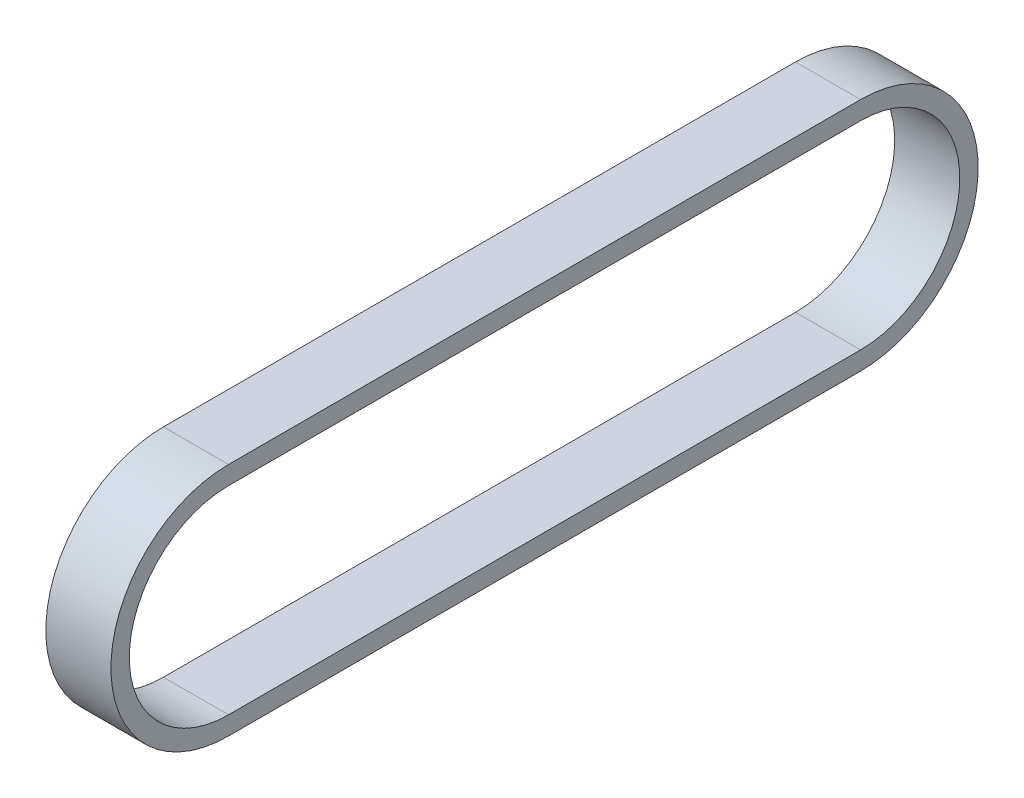
SolidWorks part; units mm, degrees
ref_plane "Front Plane" through (0, 0, 0) normal (0, 0, 1) x (1, 0, 0)
ref_plane "Top Plane" through (0, 0, 0) normal (0, 1, 0) x (1, 0, 0)
ref_plane "Right Plane" through (0, 0, 0) normal (1, 0, 0) x (0, 0, -1)
sketch "Sketch1" plane through (0, 0, 0) normal (1, 0, 0) x (0, 0, -1)
  line L0 (0, 0) -> (87.376, 0) construction
  line L1 (0, -13.716) -> (87.376, -13.716)
  line L2 (0, 13.716) -> (87.376, 13.716)
  arc A0 (0, 13.716) -> (0, -13.716) centre (0, 0) ccw
  arc A1 (87.376, -13.716) -> (87.376, 13.716) centre (87.376, 0) ccw
  dimension "D2" = 27.432
  dimension "D1" = 87.376
extrude "Extrude-Thin1" add sketch "Sketch1" along normal blind 9 thin
